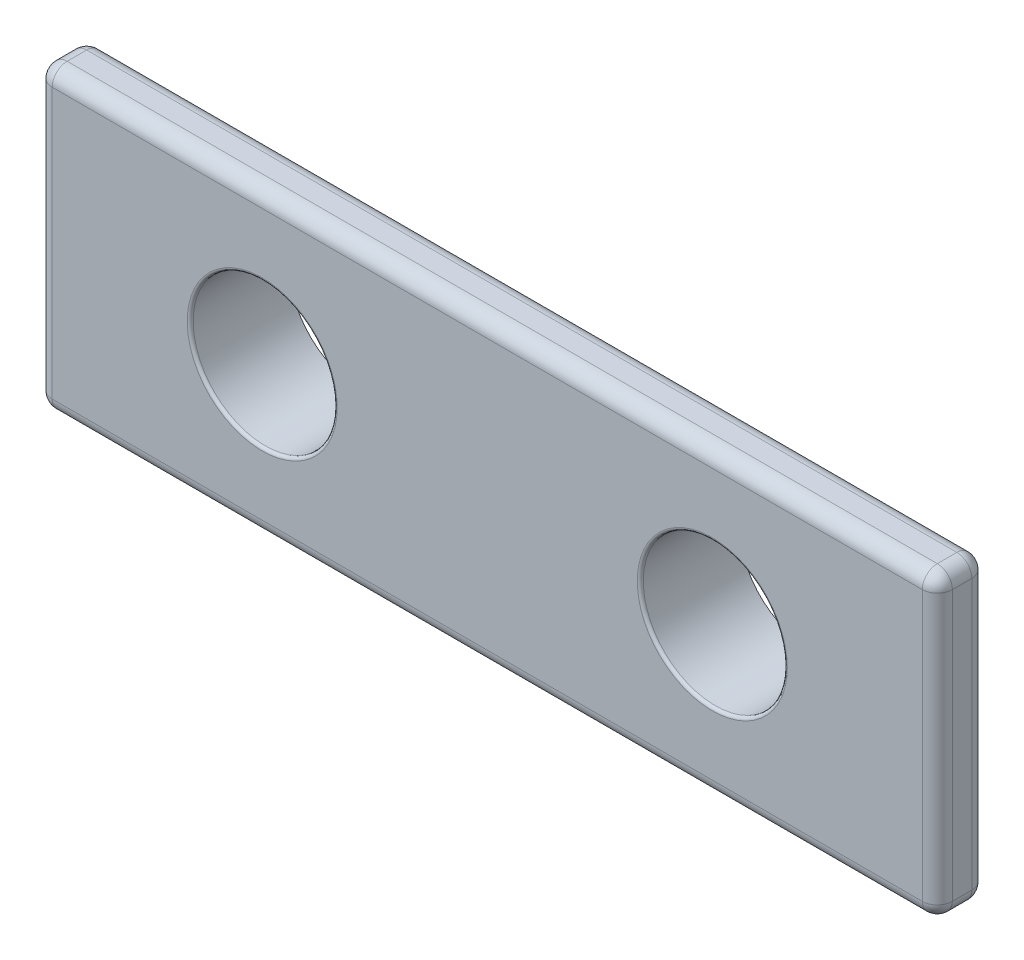
SolidWorks part; units mm, degrees
ref_plane "Front Plane" through (0, 0, 0) normal (0, 0, 1) x (1, 0, 0)
ref_plane "Top Plane" through (0, 0, 0) normal (0, 1, 0) x (1, 0, 0)
ref_plane "Right Plane" through (0, 0, 0) normal (1, 0, 0) x (0, 0, -1)
sketch "Sketch1" plane through (0, 0, 0) normal (0, 0, 1) x (1, 0, 0)
  line L0 (0, 9.998) -> (15, 0) construction
  line L1 (0, 0) -> (30, 0)
  line L2 (0, 0) -> (0, 9.998)
  line L3 (0, 9.998) -> (30, 9.998)
  line L4 (30, 0) -> (30, 9.998)
  line L5 (0, 0) -> (15, 9.998) construction
  line L6 (15, 9.998) -> (15, 0) construction
  circle A0 centre (7.5, 4.999) radius 2.4
  circle A1 centre (22.5, 4.999) radius 2.4
  dimension "D3" = 4.8
  dimension "D1" = 30
  dimension "D2" = 9.998
extrude "Boss-Extrude1" add sketch "Sketch1" along normal blind 1.65 contours L2 L3 L4 L1
sketch "Sketch2" plane through (0, 0, 0) normal (0, 0, -1) x (-1, 0, 0)
  circle A2 centre (-7.5, 4.999) radius 2.6
  circle A3 centre (-7.5, 4.999) radius 2.6
  dimension "D1" = 0.2
extrude "Boss-Extrude2" add sketch "Sketch2" along normal blind 1.65
ref_plane "Plane1" through (15, 0, 0) normal (1, 0, 0) x (0, 0, -1)
sketch "Sketch3" plane through (0, 0, 1.65) normal (0, 0, 1) x (1, 0, 0)
  circle A0 centre (7.5, 4.999) radius 2.4 construction
  circle A1 centre (7.5, 4.999) radius 2.4
extrude "Cut-Extrude1" cut sketch "Sketch3" against normal through all
fillet "Fillet1" radius 0.1 3 edges at (9.9, 4.999, 1.65) (4.9, 4.999, -1.65) (10.1, 4.999, 0)
fillet "Fillet3" radius 0.5 4 edges at (30, 9.998, 0.825) (30, 0, 0.825) (0, 9.998, 0.825) (0, 0, 0.825)
fillet "Fillet4" radius 0.5 16 edges at (29.8536, 0.1464, 1.65) (15, 0, 1.65) (0.1464, 0.1464, 1.65) (0, 4.999, 1.65) (0.1464, 9.8516, 1.65) (15, 9.998, 1.65) (29.8536, 9.8516, 1.65) (29.8536, 0.1464, 0) (15, 0, 0) (0.1464, 0.1464, 0) (0, 4.999, 0) (0.1464, 9.8516, 0) (15, 9.998, 0) (29.8536, 9.8516, 0) (30, 4.999, 1.65) (30, 4.999, 0)
mirror "Mirror2" about plane through (15, 0, 0) normal (1, 0, 0) of "Boss-Extrude2", "Cut-Extrude1", "Fillet1"
